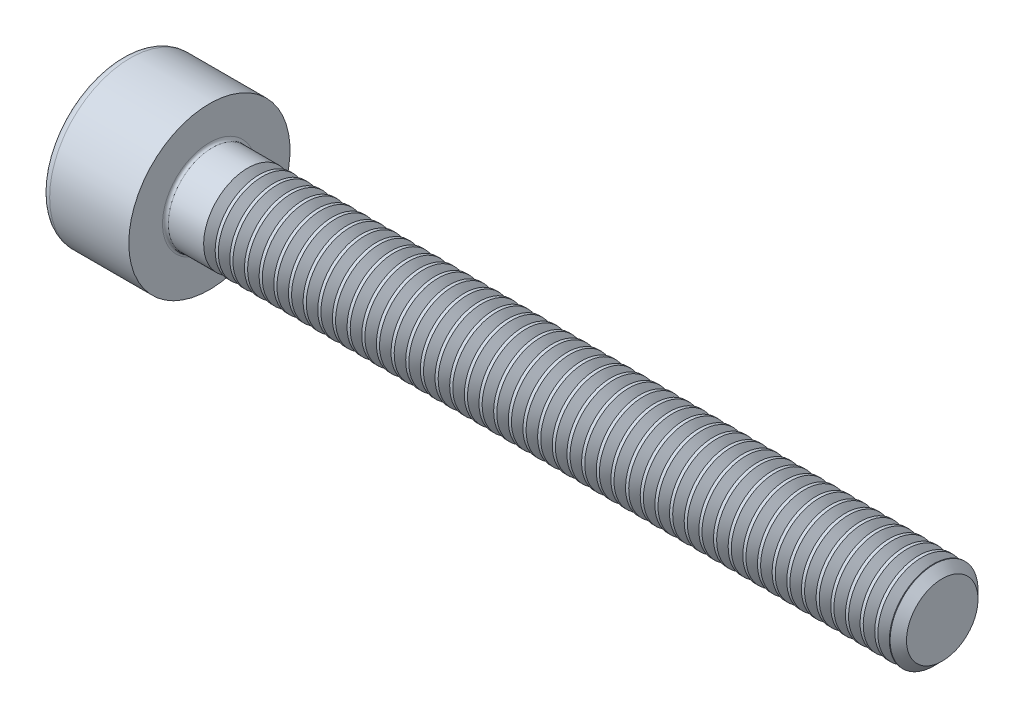
SolidWorks part; units mm, degrees
revolve "Base-Revolve" add sketch "BodySke"
sketch "BodySke" plane through (0, 0, 0) normal (0, 0, 1) x (1, 0, 0)
  line L0 (0, 0) -> (0, 2.75)
  line L1 (0, 2.75) -> (3, 2.75)
  line L2 (3, 2.75) -> (3, 1.5)
  line L3 (3, 1.5) -> (27.7195, 1.5)
  line L4 (28, 1.2195) -> (28, 0)
  line L5 (28, 0) -> (0, 0)
  line L6 (-31.75, 0) -> (127, 0) construction
  line L8 (28, 1.2195) -> (27.7195, 1.5)
  line L10 (28, -1.2195) -> (27.7195, -1.5) construction
  line L11 (3.5, 9.525) -> (3.5, 3.175) construction
  line L12 (3, 9.525) -> (3, 3.175) construction
  line L13 (-32, 9.525) -> (-32, 3.175) construction
cosmetic thread "ThreadCosmetic" [suppressed]
fillet "Fillet1" radius 0.1 1 edges at (3, 0, 1.5)
fillet "Fillet2" radius 0.3 1 edges at (0, 0, 2.75)
ref_plane "Plane1" through (0, 0, 0) normal (0, 0, 1) x (1, 0, 0)
ref_plane "Plane2" through (0, 0, 0) normal (0, 1, 0) x (1, 0, 0)
ref_plane "Plane3" through (0, 0, 0) normal (1, 0, 0) x (0, 0, -1)
sketch "Sketch2" plane through (0, 0, 0) normal (0, 0, 1) x (1, 0, 0)
  line L0 (0, 1.26) -> (1.3, 1.26)
  line L1 (1.3, 1.26) -> (2.0275, 0)
  line L2 (-31.75, 0) -> (127, 0) construction
  line L3 (2.0275, 0) -> (0, 0)
  line L4 (0, 0) -> (0, 1.26)
  line L6 (0, 0) -> (47.625, 0) construction
revolve "Hex-PreBroach" cut sketch "Sketch2" angle 360 about L6
sketch "Sketch3" plane through (0, 0, 0) normal (-1, 0, 0) x (0, 0.5, 0.866)
  line L0 (0.7275, 1.26) -> (-0.7275, 1.26)
  line L1 (-0.7275, 1.26) -> (-1.4549, 0)
  line L2 (0.7275, 1.26) -> (1.4549, 0)
  line L3 (0.7275, -1.26) -> (1.4549, 0)
  line L4 (0.7275, -1.26) -> (-0.7275, -1.26)
  line L5 (-0.7275, -1.26) -> (-1.4549, 0)
extrude "Hex" cut sketch "Sketch3" against normal blind 1.3
sketch "ThdSchSke" plane through (0, 0, 0) normal (0, 0, 1) x (1, 0, 0)
  line L0 (4.5, -1.2195) -> (4.3036, -1.5)
  line L1 (4.5, -1.2195) -> (4.6964, -1.5)
  line L2 (4.6964, -1.5) -> (4.6964, -1.875)
  line L3 (-3.175, 0) -> (5.1513, 0) construction
  line L4 (0, 2.45) -> (0, -2.45) construction
  line L5 (4.6964, -1.875) -> (4.3036, -1.875)
  line L6 (4.3036, -1.875) -> (4.3036, -1.5)
revolve "ThreadSchematic" cut sketch "ThdSchSke" angle 360 about L3
pattern_linear "ThdSchPat" count 47 spacing 0.5 along (1, 0, 0) of "ThreadSchematic"
equation "\"D2@Sketch3\" = \"Hex_size@Sketch3\" / 2"
equation "\"D1@Sketch3\" = \"Hex_size@Sketch3\" / 2"
equation "\"D1@Sketch2\" = \"Hex_size@Sketch3\" / 2"
equation "\"Thread_minor@ThreadCosmetic\"  =  \"Minor_dia@BodySke\""
equation "\"Depth@Sketch2\" =  \"Key_eng@Hex\""
equation "\"Thread_length@ThreadCosmetic\" = ((sgn( (\"Length@BodySke\" - \"Advance@BodySke\" * 3.0) - \"Thread_nom@BodySke\" )-1)*( (\"Length@BodySke\" - \"Advance@BodySke\" * 3.0) - \"Thread_nom@BodySke\" ))/-2+ \"Thread_nom@BodySke\""
equation "\"Thread_minor@ThdSchSke\" = \"Minor_dia@BodySke\""
equation "\"Diameter@ThdSchSke\" = \"Diameter@BodySke\""
equation "\"Overcut@ThdSchSke\" = \"Diameter@BodySke\" * 1.25"
equation "\"Start@ThdSchSke\" = \"Head_ht@BodySke\" + \"Length@BodySke\" - \"Thread_length@ThreadCosmetic\"  '---Non-countersunk---"
equation "\"Num_threads@ThdSchPat\" = int( \"Thread_length@ThreadCosmetic\" / \"Advance@BodySke\" + 0.999 )  + 1"
equation "\"Advance@ThdSchPat\" = \"Thread_length@ThreadCosmetic\" /  (\"Num_threads@ThdSchPat\" - 1) 'relax it"
equation "\"Num_threads@ThdSchPat\" = \"Num_threads@ThdSchPat\" - sgn( \"Num_threads@ThdSchPat\" - 1) '---chamfered tips only---"
